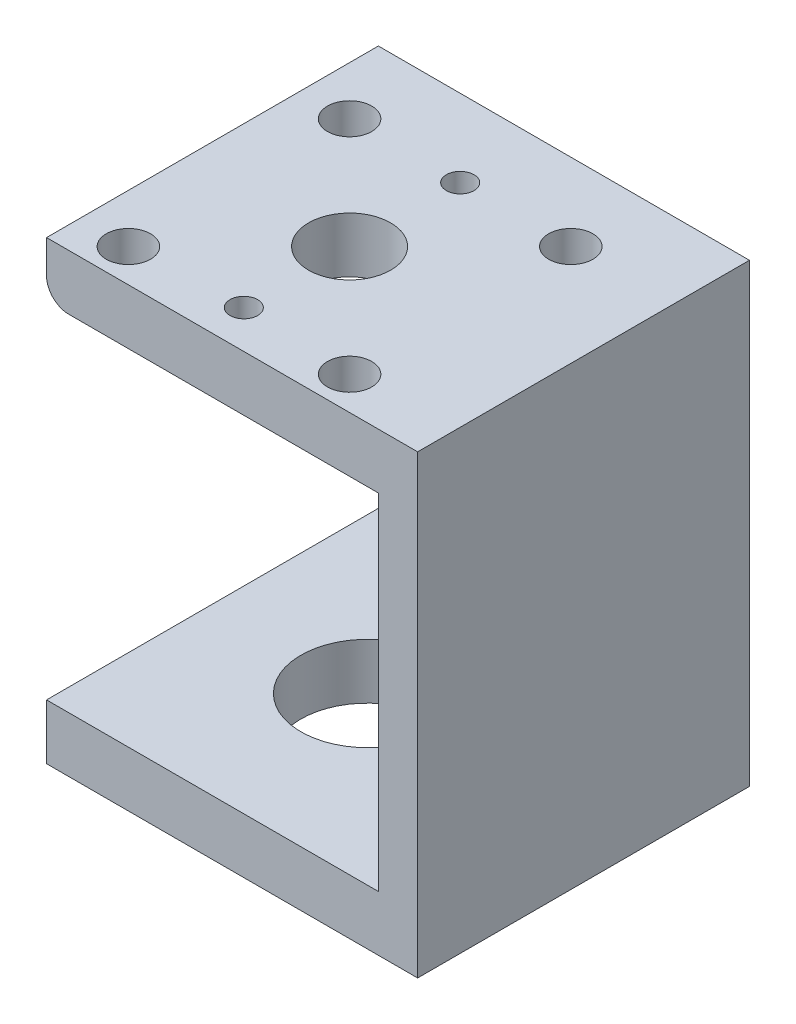
SolidWorks part; units mm, degrees
ref_plane "Alzado" through (0, 0, 0) normal (0, 0, 1) x (1, 0, 0)
ref_plane "Planta" through (0, 0, 0) normal (0, 1, 0) x (1, 0, 0)
ref_plane "Vista lateral" through (0, 0, 0) normal (1, 0, 0) x (0, 0, -1)
sketch "Croquis1" plane through (0, 0, 0) normal (0, 1, 0) x (1, 0, 0)
  line L1 (-16.7763, -15) -> (16.7763, -15)
  line L2 (-16.7763, -15) -> (-16.7763, 15)
  line L3 (-16.7763, 15) -> (16.7763, 15)
  line L4 (16.7763, -15) -> (16.7763, 15)
  line L5 (-16.7763, -15) -> (16.7763, 15) construction
  line L6 (-16.7763, 15) -> (16.7763, -15) construction
  point P0 (0, 0)
  dimension "D1" = 30
extrude "Saliente-Extruir1" add sketch "Croquis1" along normal blind 41.2 contours L1 L4 L3 L2
sketch "Croquis2" plane through (0, 0, 15) normal (0, 0, 1) x (1, 0, 0)
  line L0 (-16.7763, 41.2) -> (-16.7763, 0) construction
  line L1 (-16.7763, 36.2) -> (13.2237, 36.2)
  line L2 (-16.7763, 36.2) -> (-16.7763, 5)
  line L3 (-16.7763, 5) -> (13.2237, 5)
  line L4 (13.2237, 36.2) -> (13.2237, 5)
  line L5 (16.5, 0) -> (-16.5, 0) construction
  dimension "D1" = 31.2
  dimension "D2" = 5
  dimension "D3" = 30
extrude "Cortar-Extruir1" cut sketch "Croquis2" against normal blind 36.2
sketch "Croquis3" plane through (0, 41.2, 0) normal (0, 1, 0) x (1, 0, 0)
  line L0 (-16.7763, -15) -> (-16.7763, 15) construction
  line L2 (-16.7763, 15) -> (16.7763, 15) construction
  circle A0 centre (-12.3763, -12) radius 2
  circle A1 centre (-2.3763, -11.5633) radius 1.25
  circle A2 centre (7.6237, -12) radius 2
  circle A3 centre (-2.3763, -2) radius 3.71
  circle A4 centre (7.6237, 8) radius 2
  circle A5 centre (-2.3763, 8) radius 1.25
  circle A6 centre (-12.3763, 8) radius 2
  dimension "D1" = 7.42
  dimension "D2" = 4
  dimension "D3" = 2.5
  dimension "D4" = 10
  dimension "D5" = 10
  dimension "D6" = 20
  dimension "D7" = 4.4
  dimension "D8" = 7
  dimension "D9" = 20
  dimension "D10" = 10
extrude "Cortar-Extruir2" cut sketch "Croquis3" against normal blind 5
sketch "Croquis4" plane through (0, 0, 0) normal (0, -1, 0) x (1, 0, 0)
  line L1 (-16.7763, 15) -> (-16.7763, -15) construction
  circle A0 centre (-2.78, 0) radius 6
  dimension "D1" = 12
  dimension "D2" = 13.9963
extrude "Cortar-Extruir3" cut sketch "Croquis4" against normal blind 5
fillet "Redondeo1" radius 2 1 edges at (-16.7763, 36.2, 0)
